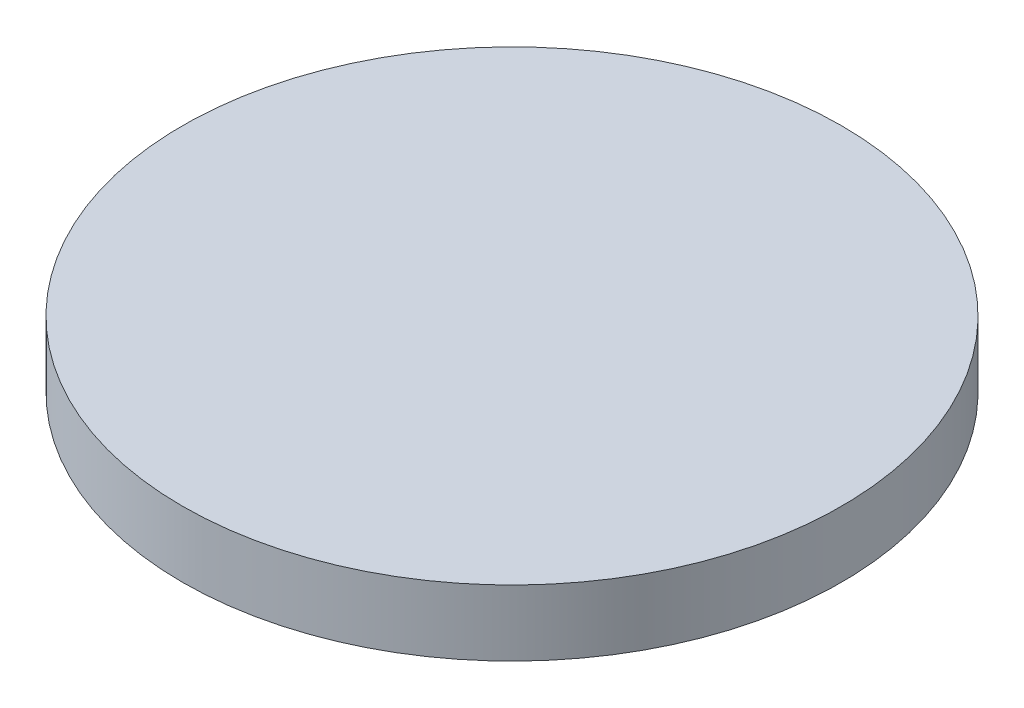
SolidWorks part; units mm, degrees
ref_plane "Front Plane" through (0, 0, 0) normal (0, 0, 1) x (1, 0, 0)
ref_plane "Top Plane" through (0, 0, 0) normal (0, 1, 0) x (1, 0, 0)
ref_plane "Right Plane" through (0, 0, 0) normal (1, 0, 0) x (0, 0, -1)
sketch "Sketch1" plane through (0, 0, 0) normal (0, 1, 0) x (1, 0, 0)
  circle A0 centre (0, 0) radius 5
extrude "Boss-Extrude1" add sketch "Sketch1" along normal blind 1
